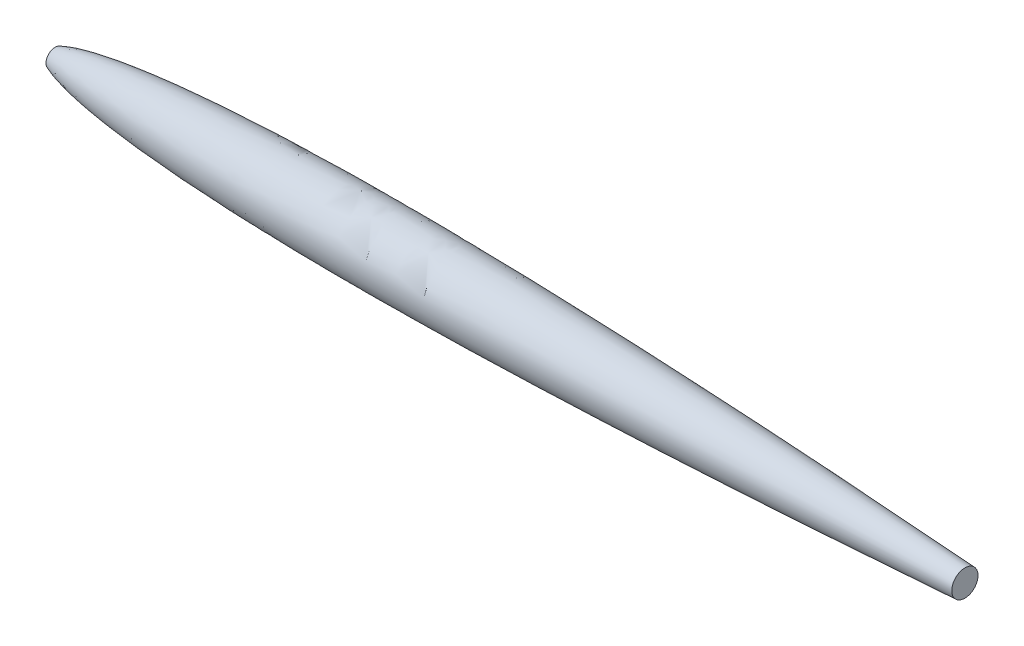
SolidWorks part; units mm, degrees
ref_plane "Front Plane" through (0, 0, 0) normal (0, 0, 1) x (1, 0, 0)
ref_plane "Top Plane" through (0, 0, 0) normal (0, 1, 0) x (1, 0, 0)
ref_plane "Right Plane" through (0, 0, 0) normal (1, 0, 0) x (0, 0, -1)
sketch "rootSketch" plane through (0, 0, 0) normal (0, 1, 0) x (1, 0, 0)
  line L0 (0, 0) -> (12000, 0) construction
  line L1 (2750, -330) -> (2750, 330) construction
  line L2 (0, 0) -> (11000, 0)
  spline S0 degree 4 poles (0, 0) (0.0002, 1.4166) (0.1225, 4.2408) (0.6739, 8.4547) (2.1097, 13.9385) (4.13, 19.1147) (6.6109, 23.9643) (9.9914, 29.3681) (13.8074, 34.3715) (18.0051, 39.0824) (24.0066, 45.0125) (32.3839, 52.2354) (43.384, 60.1944) (57.0761, 68.6181) (73.983, 77.7243) (92.7893, 86.6435) (113.9578, 95.5167) (137.4556, 104.3111) (166.2995, 114.136) (201.291, 124.8338) (243.0702, 136.2047) (291.673, 147.964) (341.2433, 158.778) (390.608, 168.603) (439.7192, 177.609) (500.6517, 187.9807) (573.4692, 199.2826) (658.6122, 211.1866) (758.0842, 223.6079) (859.6848, 234.9957) (963.387, 245.4645) (1069.1706, 255.1028) (1175.0326, 263.8354) (1280.9578, 271.7615) (1386.9346, 278.9616) (1492.954, 285.5022) (1625.577, 292.9263) (1784.8272, 300.7239) (1970.7211, 308.3762) (2183.2661, 315.3874) (2395.8558, 320.8604) (2608.4762, 324.9557) (2821.1167, 327.8069) (3033.7692, 329.5269) (3299.5919, 330.3841) (3618.5808, 329.5138) (3990.7204, 326.0523) (4415.9852, 319.2091) (4841.2016, 309.8574) (5266.3634, 298.3074) (5691.4677, 284.8151) (6116.5132, 269.5907) (6541.4998, 252.8057) (6966.4276, 234.5973) (7391.2968, 215.0715) (7816.1072, 194.3061) (8187.764, 175.0965) (8506.2884, 157.9049) (8771.6988, 143.0951) (8984.0106, 130.9561) (9196.3055, 118.5234) (9382.048, 107.3844) (9541.2445, 97.6474) (9673.9002, 89.4049) (9780.02, 82.7331) (9912.6633, 74.2947) (10032.035, 66.5803) (10138.1364, 59.6277) (10230.971, 53.4713) (10284.0168, 49.9324) (10337.0641, 46.3721) (10390.1043, 42.7909) (10443.153, 39.1874) (10496.1834, 35.5635) (10549.2402, 31.9155) (10602.2495, 28.2488) (10655.3329, 24.5543) (10708.2897, 20.8463) (10761.4536, 17.1004) (10814.2582, 13.3575) (10861.0394, 10.0201) (10900.2084, 7.2123) (10934.3368, 4.7545) (10958.871, 2.9835) (10991.7181, 0.6028) (11015.0262, -1.0918) (11049.9588, -3.6388) (11071.8096, -5.2409) (11099.5819, -7.2784) (11124.1625, -9.0892) (11155.0411, -11.3693) (11188.9639, -13.8862) (11223.5859, -16.4645) (11266.4367, -19.6696) (11318.0968, -23.5545) (11369.6077, -27.4555) (11421.2086, -31.3904) (11472.7604, -35.3439) (11524.3346, -39.3212) (11584.4862, -43.9929) (11670.4236, -50.7243) (11756.3495, -57.532) (11842.2728, -64.4184) (11928.1873, -71.3847) (11996.9163, -77.0066) (12048.459, -81.2601) (12082.8201, -84.1126) (12100, -85.543) knots 0 0 0 0 0 0.000464 0.000929 0.001393 0.001858 0.002287 0.002716 0.003486 0.003922 0.004359 0.005488 0.007118 0.008378 0.009638 0.011797 0.013955 0.015919 0.017882 0.02181 0.025978 0.030146 0.034314 0.038482 0.042518 0.046554 0.054626 0.062698 0.07077 0.079497 0.088224 0.096952 0.105679 0.114406 0.123133 0.13186 0.140587 0.158059 0.17553 0.193002 0.210474 0.227946 0.245418 0.26289 0.280362 0.315306 0.35025 0.385194 0.420137 0.455081 0.490025 0.524969 0.559913 0.594857 0.6298 0.664744 0.699688 0.71716 0.734632 0.752104 0.769576 0.787048 0.795784 0.80452 0.813256 0.821992 0.839464 0.843832 0.8482 0.852567 0.856935 0.861303 0.865671 0.870039 0.874407 0.878775 0.883143 0.887511 0.891879 0.896247 0.900615 0.902799 0.904983 0.907167 0.909351 0.912184 0.915017 0.916433 0.91785 0.920682 0.923515 0.926348 0.929181 0.932013 0.937679 0.943345 0.946177 0.94901 0.954676 0.960341 0.966007 0.977338 0.983003 0.988669 0.994334 1 1 1 1 1 construction
  spline S1 degree 4 poles (0, 0) (0.0002, 1.4166) (0.1225, 4.2408) (0.6739, 8.4547) (2.1097, 13.9385) (4.13, 19.1147) (6.6109, 23.9643) (9.9914, 29.3681) (13.8074, 34.3715) (18.0051, 39.0824) (24.0066, 45.0125) (32.3839, 52.2354) (43.384, 60.1944) (57.0761, 68.6181) (73.983, 77.7243) (92.7893, 86.6435) (113.9578, 95.5167) (137.4556, 104.3111) (166.2995, 114.136) (201.291, 124.8338) (243.0702, 136.2047) (291.673, 147.964) (341.2433, 158.778) (390.608, 168.603) (439.7192, 177.609) (500.6517, 187.9807) (573.4692, 199.2826) (658.6122, 211.1866) (758.0842, 223.6079) (859.6848, 234.9957) (963.387, 245.4645) (1069.1706, 255.1028) (1175.0326, 263.8354) (1280.9578, 271.7615) (1386.9346, 278.9616) (1492.954, 285.5022) (1625.577, 292.9263) (1784.8272, 300.7239) (1970.7211, 308.3762) (2183.2661, 315.3874) (2395.8558, 320.8604) (2608.4762, 324.9557) (2821.1167, 327.8069) (3033.7692, 329.5269) (3299.5919, 330.3841) (3618.5808, 329.5138) (3990.7204, 326.0523) (4415.9852, 319.2091) (4841.2016, 309.8574) (5266.3634, 298.3074) (5691.4677, 284.8151) (6116.5132, 269.5907) (6541.4998, 252.8057) (6966.4276, 234.5973) (7391.2968, 215.0715) (7816.1072, 194.3061) (8187.764, 175.0965) (8506.2884, 157.9049) (8771.6988, 143.0951) (8984.0106, 130.9561) (9196.3055, 118.5234) (9382.048, 107.3844) (9541.2445, 97.6474) (9673.9002, 89.4049) (9780.02, 82.7331) (9912.6633, 74.2947) (10032.035, 66.5803) (10138.1364, 59.6277) (10230.971, 53.4713) (10284.0168, 49.9324) (10337.0641, 46.3721) (10390.1043, 42.7909) (10443.153, 39.1874) (10496.1834, 35.5635) (10549.2402, 31.9155) (10602.2495, 28.2488) (10655.3329, 24.5543) (10708.2897, 20.8463) (10761.4536, 17.1004) (10814.2582, 13.3575) (10861.0394, 10.0201) (10900.2084, 7.2123) (10934.3368, 4.7545) (10958.871, 2.9835) (10981.8033, 1.3214) (10993.9727, 0.438) (11000, 0) knots 0 0 0 0 0 0.000464 0.000929 0.001393 0.001858 0.002287 0.002716 0.003486 0.003922 0.004359 0.005488 0.007118 0.008378 0.009638 0.011797 0.013955 0.015919 0.017882 0.02181 0.025978 0.030146 0.034314 0.038482 0.042518 0.046554 0.054626 0.062698 0.07077 0.079497 0.088224 0.096952 0.105679 0.114406 0.123133 0.13186 0.140587 0.158059 0.17553 0.193002 0.210474 0.227946 0.245418 0.26289 0.280362 0.315306 0.35025 0.385194 0.420137 0.455081 0.490025 0.524969 0.559913 0.594857 0.6298 0.664744 0.699688 0.71716 0.734632 0.752104 0.769576 0.787048 0.795784 0.80452 0.813256 0.821992 0.839464 0.843832 0.8482 0.852567 0.856935 0.861303 0.865671 0.870039 0.874407 0.878775 0.883143 0.887511 0.891879 0.896247 0.900615 0.902799 0.904983 0.907167 0.909351 0.909351 0.909351 0.909351 0.909351
  point P5 (2750, 0)
  dimension "rootQuarterChord" = 2750
  dimension "rootMaxThickness" = 660
revolve "Revolve1" add sketch "rootSketch" angle 360 about L0
ref_plane "Plane1" through (9020, 0, 0) normal (1, 0, 0) x (0, 0, -1)
sketch "cutSketch" plane through (9020, 0, 0) normal (1, 0, 0) x (0, 0, -1)
  circle A0 centre (0, 0) radius 330
  dimension "cutDiameter" = 660
extrude "Cut-Extrude1" cut sketch "cutSketch" along normal through all
sketch "Sketch1" plane through (0, 0, 0) normal (1, 0, 0) x (0, 0, -1)
  circle A0 centre (0, 0) radius 330
  dimension "D1" = 660
extrude "Cut-Extrude2" cut sketch "Sketch1" along normal blind 100 contours A0
equation "\"chord\"= 11.00"
equation "\"NACAairfoil\"= 0006"
equation "\"tailCutoffPercentage\"= 0.18"
equation "\"rootQuarterChord@rootSketch\"=\"chord\"/4"
equation "\"rootMaxThickness@rootSketch\"= \"rootQuarterChord@rootSketch\" * 4 * \"NACAairfoil\" / 100"
equation "\"cutDiameter@cutSketch\"=\"rootMaxThickness@rootSketch\""
equation "\"cutChord@Plane1\"= \"rootQuarterChord@rootSketch\" * 4 * ( 1 - \"tailCutoffPercentage\" )"
equation "\"D1@Sketch1\"=\"rootMaxThickness@rootSketch\""
